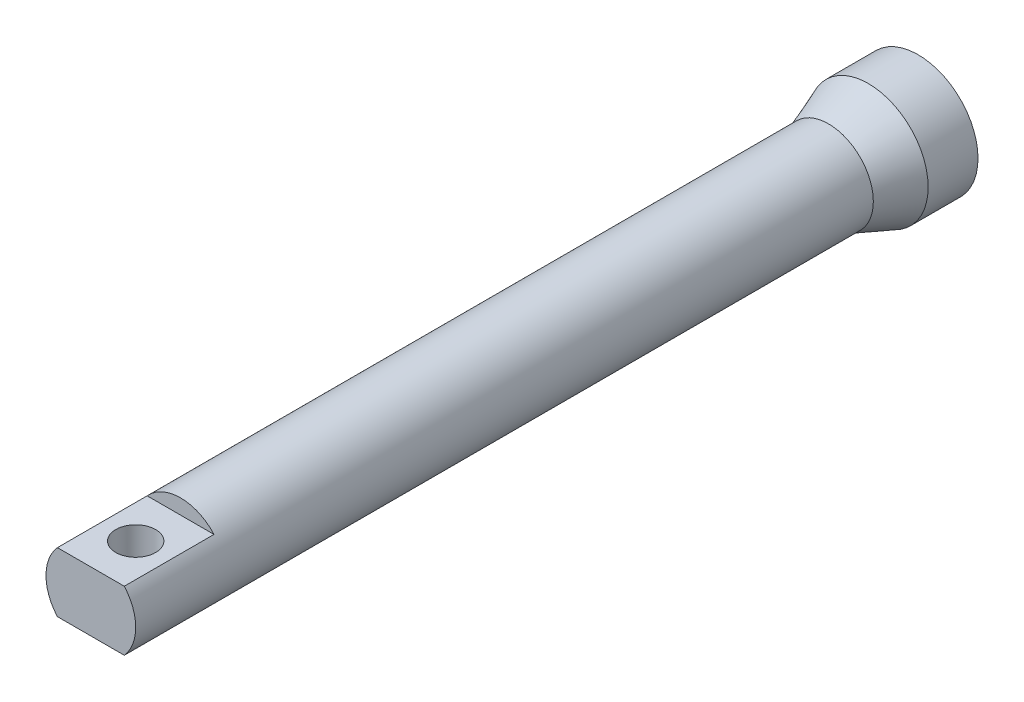
SolidWorks part; units mm, degrees
ref_plane "Front Plane" through (0, 0, 0) normal (0, 0, 1) x (1, 0, 0)
ref_plane "Top Plane" through (0, 0, 0) normal (0, 1, 0) x (1, 0, 0)
ref_plane "Right Plane" through (0, 0, 0) normal (1, 0, 0) x (0, 0, -1)
sketch "Sketch2" plane through (0, 0, 0) normal (0, 1, 0) x (1, 0, 0)
  line L0 (-30, 0) -> (0, 0) construction
  line L1 (-30, 0) -> (-30, -25)
  line L2 (-30, -25) -> (-22.5, -45)
  line L3 (-30, 0) -> (-25, 0)
  line L4 (-25, 0) -> (-25, -25)
  line L5 (-25, -25) -> (-17.5, -45)
  line L6 (-17.5, -45) -> (-22.5, -45)
  dimension "D1" = 30
  dimension "D2" = 20
  dimension "D3" = 25
  dimension "D4" = 22.5
  dimension "D5" = 5
  dimension "D6" = 5
  dimension "D7" = 5
ref_axis "Axis1" through (0, 0, 47.25) along (0, 0, -1)
revolve "Revolve1" add sketch "Sketch2" angle 360 about axis through (0, 0, 47.25) along (0, 0, -1)
sketch "Sketch3" plane through (0, 0, 45) normal (0, 0, 1) x (1, 0, 0)
  circle A0 centre (0, 0) radius 17.5 construction
  circle A1 centre (0, 0) radius 22.5 construction
  circle A2 centre (0, 0) radius 17.5
  circle A3 centre (0, 0) radius 22.5
extrude "Boss-Extrude1" add sketch "Sketch3" along normal blind 320
sketch "Sketch4" plane through (0, 0, 365) normal (0, 0, 1) x (1, 0, 0)
  circle A0 centre (0, 0) radius 22.5 construction
  circle A1 centre (0, 0) radius 22.5
extrude "Boss-Extrude2" add sketch "Sketch4" along normal blind 50
sketch "Sketch5" plane through (0, 0, 415) normal (0, 0, 1) x (1, 0, 0)
  line L0 (-50, 15) -> (50, 15) construction
  line L1 (50, 15) -> (50, -15) construction
  line L2 (50, -15) -> (-50, -15) construction
  line L3 (-50, -15) -> (-50, 15) construction
  line L4 (-50, 15) -> (50, -15) construction
  line L5 (-50, -15) -> (50, 15) construction
  line L6 (24.75, 0) -> (-24.75, 0) construction
  line L7 (16.7705, 15) -> (-16.7705, 15)
  line L8 (16.7705, 15) -> (16.7705, 35)
  line L9 (16.7705, 35) -> (-16.7705, 35)
  line L10 (-16.7705, 15) -> (-16.7705, 35)
  line L11 (16.7705, -35) -> (-16.7705, -35)
  line L12 (-16.7705, -15) -> (-16.7705, -35)
  line L13 (16.7705, -15) -> (-16.7705, -15)
  line L14 (16.7705, -15) -> (16.7705, -35)
  circle A0 centre (0, 0) radius 22.5 construction
  circle A1 centre (0, 0) radius 22.5 construction
  point P2 (0, 0)
  dimension "D1" = 30
  dimension "D2" = 100
extrude "Cut-Extrude1" cut sketch "Sketch5" against normal blind 45
sketch "Sketch6" plane through (0, 15, 0) normal (0, 1, 0) x (1, 0, 0)
  line L0 (-16.7705, -370) -> (16.7705, -415) construction
  line L4 (-16.7705, -415) -> (16.7705, -415)
  line L5 (16.7705, -415) -> (16.7705, -370)
  line L6 (16.7705, -370) -> (-16.7705, -370)
  line L7 (-16.7705, -370) -> (-16.7705, -415)
  line L8 (-16.7705, -415) -> (16.7705, -415)
  line L9 (16.7705, -415) -> (16.7705, -370)
  line L10 (16.7705, -370) -> (-16.7705, -370)
  line L11 (-16.7705, -370) -> (-16.7705, -415)
  circle A0 centre (0, -392.5) radius 10
  dimension "D2" = 20
  dimension "D1" = 0
extrude "Cut-Extrude3" cut sketch "Sketch6" against normal through all both and the other way through all contours A0
equation "\"wideTopWidth\"= 60mm"
equation "\"D1@Sketch2\"=\"wideTopWidth\"/2"
equation "\"tubeWidth\"= 45mm"
equation "\"wallThickness\"= 5mm"
equation "\"D4@Sketch2\"=\"tubeWidth\"/2"
equation "\"D5@Sketch2\"=\"wallThickness\""
equation "\"D7@Sketch2\"=\"wallThickness\""
equation "\"D6@Sketch2\"=\"wallThickness\""
equation "\"tubeFullLen\"= 370mm"
equation "\"D1@Boss-Extrude1\"=\"tubeFullLen\"-50"
equation "\"D1@Boss-Extrude2\"=50"
